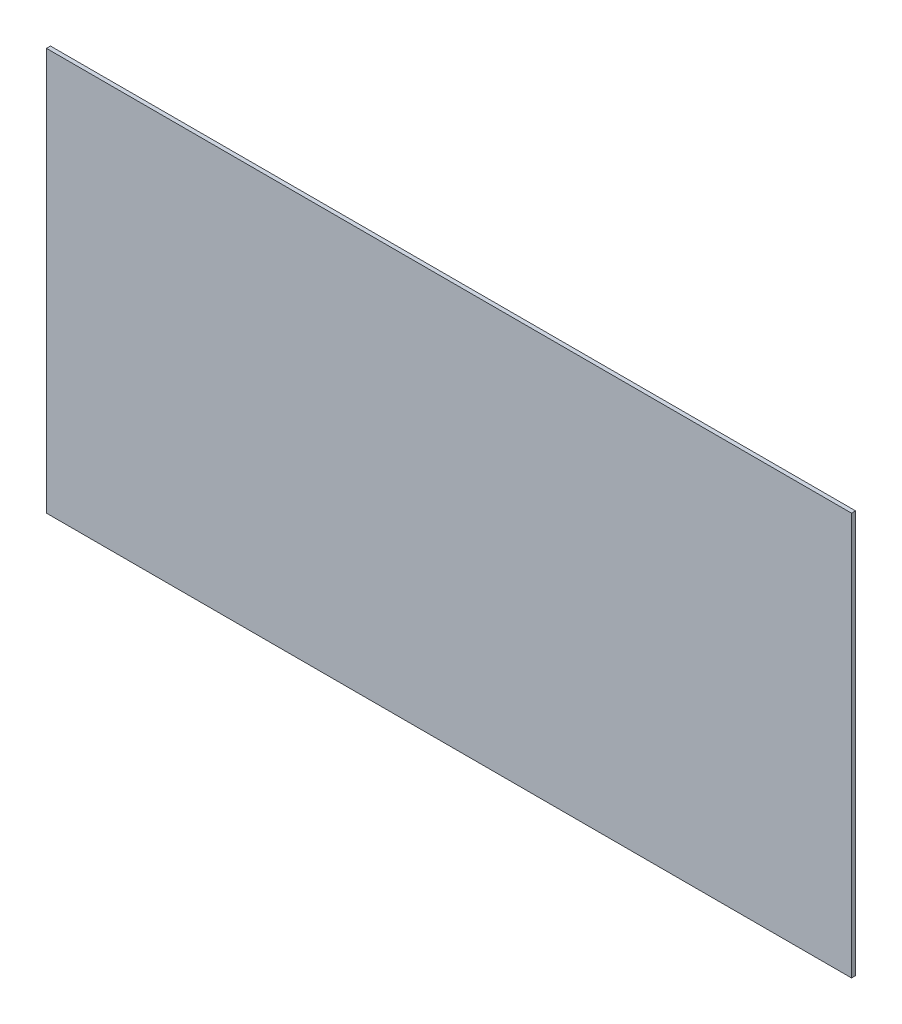
SolidWorks part; units mm, degrees
ref_plane "Alzado" through (0, 0, 0) normal (0, 0, 1) x (1, 0, 0)
ref_plane "Planta" through (0, 0, 0) normal (0, 1, 0) x (1, 0, 0)
ref_plane "Vista lateral" through (0, 0, 0) normal (1, 0, 0) x (0, 0, -1)
sketch "Croquis1" plane through (0, 0, 0) normal (0, 0, 1) x (1, 0, 0)
  line L6 (0, 0) -> (600, 0)
  line L7 (0, 0) -> (0, 300)
  line L8 (0, 300) -> (600, 300)
  line L9 (600, 0) -> (600, 300)
  dimension "D1" = 600
  dimension "D2" = 300
extrude "Saliente-Extruir1" add sketch "Croquis1" along normal blind 3
